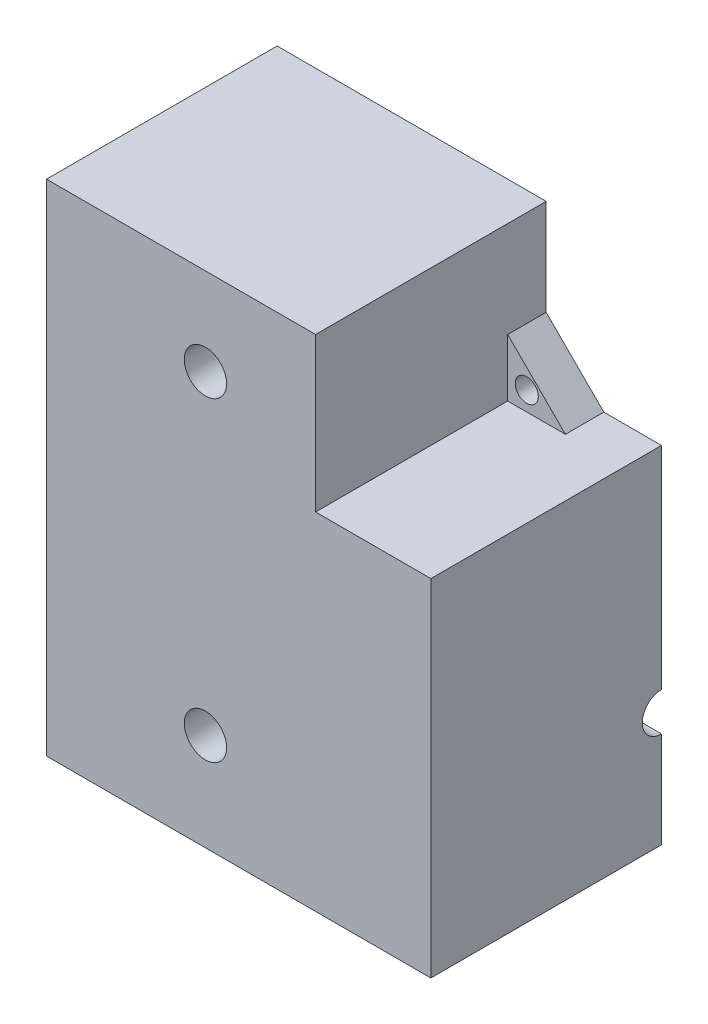
SolidWorks part; units mm, degrees
ref_plane "Front" through (0, 0, 0) normal (0, 0, 1) x (1, 0, 0)
ref_plane "Top" through (0, 0, 0) normal (0, 1, 0) x (1, 0, 0)
ref_plane "Right" through (0, 0, 0) normal (1, 0, 0) x (0, 0, -1)
sketch "Sketch1" plane through (0, 0, 0) normal (0, 0, 1) x (1, 0, 0)
  line L0 (-27.6704, -25.6577) -> (-27.6704, -38.1577)
  line L1 (-62.6704, -25.6577) -> (-27.6704, -25.6577)
  line L2 (-62.6704, -25.6577) -> (-62.6704, -53.1577)
  line L3 (-62.6704, -90.6577) -> (-42.6704, -90.6577)
  line L4 (-12.6704, -90.6577) -> (-12.6704, -45.6577)
  line L5 (-12.6704, -45.6577) -> (-20.1704, -45.6577)
  line L6 (-62.6704, -90.6577) -> (-62.6704, -63.1577)
  line L7 (-27.6704, -38.1577) -> (-20.1704, -45.6577)
  line L8 (-12.6704, -90.6577) -> (-32.6704, -90.6577)
  line L17 (-42.6704, -90.6577) -> (-37.6704, -96.7077)
  line L18 (-62.6704, -53.1577) -> (-68.7192, -58.1577)
  line L19 (-68.7192, -58.1577) -> (-62.6704, -63.1577)
  line L20 (-32.6704, -90.6577) -> (-37.6704, -96.7077)
extrude "Base-Extrude" add sketch "Sketch1" along normal blind 5
sketch "Sketch2" plane through (0, 0, 5) normal (0, 0, 1) x (1, 0, 0)
  line L0 (-57.6704, -55.5117) -> (-57.6704, -60.8036)
  line L1 (-40.3161, -85.6577) -> (-35.0248, -85.6577)
  line L2 (-32.6704, -40.2287) -> (-32.6704, -50.6577)
  line L3 (-32.6704, -50.6577) -> (-22.2415, -50.6577)
  line L12 (-57.6704, -30.6577) -> (-57.6704, -55.5117)
  line L13 (-57.6704, -30.6577) -> (-57.6704, -55.5117)
  line L14 (-17.6704, -50.6577) -> (-22.2415, -50.6577)
  line L15 (-57.6704, -55.5117) -> (-60.8714, -58.1577)
  line L17 (-32.6704, -30.6577) -> (-57.6704, -30.6577)
  line L18 (-60.8714, -58.1577) -> (-57.6704, -60.8036)
  line L20 (-17.6704, -50.6577) -> (-22.2415, -50.6577)
  line L21 (-57.6704, -60.8036) -> (-57.6704, -85.6577)
  line L23 (-32.6704, -30.6577) -> (-57.6704, -30.6577)
  line L26 (-57.6704, -60.8036) -> (-57.6704, -85.6577)
  line L27 (-57.6704, -85.6577) -> (-40.3161, -85.6577)
  line L28 (-57.6704, -85.6577) -> (-40.3161, -85.6577)
  line L29 (-40.3161, -85.6577) -> (-37.6704, -88.8589)
  line L31 (-32.6704, -40.2287) -> (-32.6704, -30.6577)
  line L32 (-32.6704, -40.2287) -> (-32.6704, -30.6577)
  line L33 (-37.6704, -88.8589) -> (-35.0248, -85.6577)
  line L35 (-35.0248, -85.6577) -> (-17.6704, -85.6577)
  line L36 (-35.0248, -85.6577) -> (-17.6704, -85.6577)
  line L37 (-17.6704, -85.6577) -> (-17.6704, -50.6577)
  line L38 (-17.6704, -85.6577) -> (-17.6704, -50.6577)
  line L39 (-22.2415, -50.6577) -> (-32.6704, -40.2287)
  dimension "D1" = 5
sketch "Sketch12" plane through (0, 0, 5) normal (0, 0, 1) x (1, 0, 0)
  circle A0 centre (-65.2192, -58.1577) radius 1.5
  circle A1 centre (-37.6704, -93.2077) radius 1.5
  circle A2 centre (-25.1956, -43.1828) radius 1.5
extrude "Cut-Extrude11" cut sketch "Sketch12" against normal blind 10
cosmetic thread "Cosmetic Thread7" parameters "D1"=5, "D2"=4
cosmetic thread "Cosmetic Thread8" parameters "D1"=5, "D2"=4
cosmetic thread "Cosmetic Thread9" parameters "D1"=5, "D2"=4
sketch "Sketch13" plane through (0, 0, 5) normal (0, 0, 1) x (1, 0, 0)
  line L0 (-62.6704, -25.6577) -> (-62.6704, -90.6577)
  line L1 (-62.6704, -90.6577) -> (-12.6704, -90.6577)
  line L2 (-12.6704, -90.6577) -> (-12.6704, -45.6577)
  line L3 (-62.6704, -25.6577) -> (-27.6704, -25.6577)
  line L4 (-27.6704, -25.6577) -> (-27.6704, -45.6577)
  line L5 (-27.6704, -45.6577) -> (-12.6704, -45.6577)
extrude "Boss-Extrude1" add sketch "Sketch13" along normal blind 25
extrude "Cut-Extrude14" cut sketch "Sketch2" against normal blind 20
sketch "Sketch14" plane through (0, 0, 5) normal (0, 0, -1) x (-1, 0, 0)
  line L0 (32.6704, -30.6577) -> (57.6704, -30.6577)
  line L1 (57.6704, -30.6577) -> (57.6704, -85.6577)
  line L2 (57.6704, -85.6577) -> (17.6704, -85.6577)
  line L3 (17.6704, -85.6577) -> (17.6704, -50.6577)
  line L4 (17.6704, -50.6577) -> (32.6704, -50.6577)
  line L5 (32.6704, -50.6577) -> (32.6704, -30.6577)
extrude "Cut-Extrude15" cut sketch "Sketch14" against normal blind 20
sketch "Sketch15" plane through (0, 0, 30) normal (0, 0, 1) x (1, 0, 0)
  circle A0 centre (45, -75.6577) radius 2.75
  circle A1 centre (-42, -78) radius 2.75
extrude "Cut-Extrude16" cut sketch "Sketch15" against normal blind 20
sketch "Sketch16" plane through (-12.6704, 0, 0) normal (1, 0, 0) x (0, 0, -1)
  circle A0 centre (0, -75.6577) radius 2.5
extrude "Extrude1" cut sketch "Sketch16" against normal blind 10
sketch "Sketch17" plane through (0, 0, 25) normal (0, 0, -1) x (-1, 0, 0)
  circle A0 centre (42, -37) radius 2.75
extrude "Extrude2" cut sketch "Sketch17" against normal blind 6
